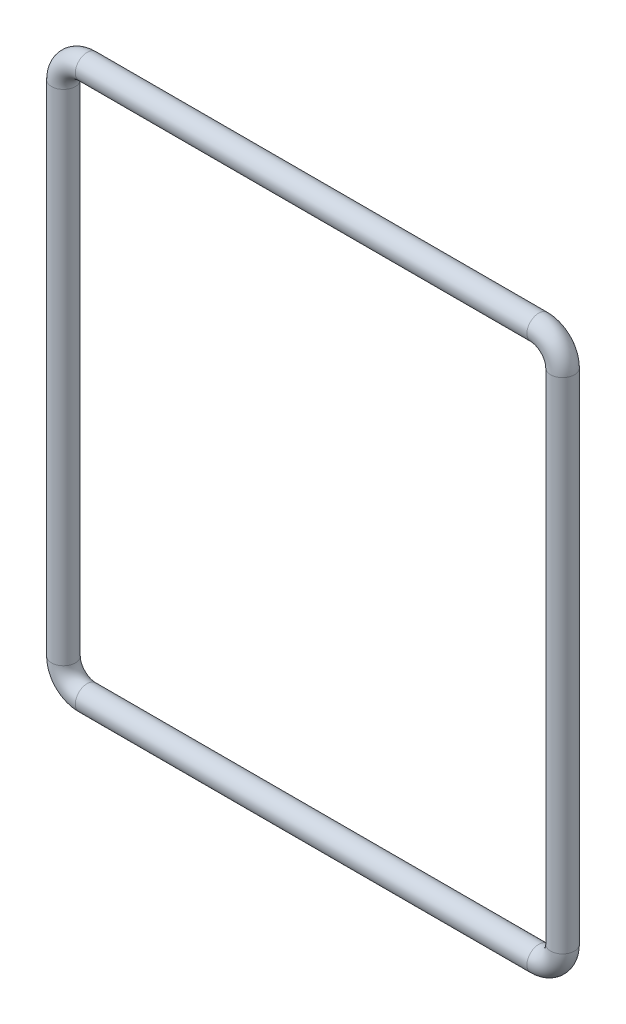
SolidWorks part; units mm, degrees
ref_plane "Face" through (0, 0, 0) normal (0, 0, 1) x (1, 0, 0)
ref_plane "Dessus" through (0, 0, 0) normal (0, 1, 0) x (1, 0, 0)
ref_plane "Droite" through (0, 0, 0) normal (1, 0, 0) x (0, 0, -1)
sketch "Esquisse1" plane through (0, 0, 0) normal (0, 0, 1) x (1, 0, 0)
  line L1 (-19, 23) -> (19, 23)
  line L2 (-21, 21) -> (-21, -21)
  line L3 (-19, -23) -> (19, -23)
  line L4 (21, 21) -> (21, -21)
  arc A0 (-21, -21) -> (-19, -23) centre (-19, -21) ccw
  arc A1 (-19, 23) -> (-21, 21) centre (-19, 21) ccw
  arc A2 (19, 23) -> (21, 21) centre (19, 21) cw
  arc A3 (19, -23) -> (21, -21) centre (19, -21) ccw
  point P4 (0, 23)
  point P6 (21, 0)
  point P11 (-21, 23)
  point P14 (21, 23)
  point P17 (21, -23)
  dimension "D3" = 2
  dimension "D4" = 2
  dimension "D1" = 46
  dimension "D2" = 42
sketch "Esquisse2" plane through (0, 0, 0) normal (0, 1, 0) x (1, 0, 0)
  circle A0 centre (21, 0) radius 1
  dimension "D1" = 2
sweep "Balayage1" add profiles "Esquisse2" path "Esquisse1"
